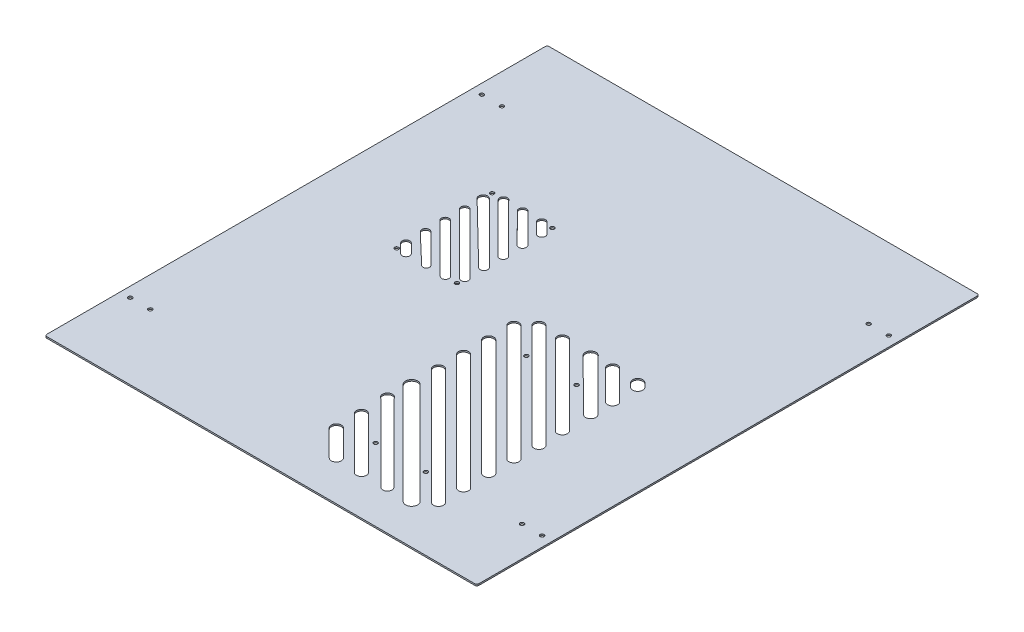
SolidWorks part; units mm, degrees
ref_plane "Front Plane" through (0, 0, 0) normal (0, 0, 1) x (1, 0, 0)
ref_plane "Top Plane" through (0, 0, 0) normal (0, 1, 0) x (1, 0, 0)
ref_plane "Right Plane" through (0, 0, 0) normal (1, 0, 0) x (0, 0, -1)
other "Center of Mass"
sketch "Sketch1" plane through (0, 0, 0) normal (0, 1, 0) x (1, 0, 0)
  line L1 (-215, -250) -> (215, -250)
  line L2 (-215, -250) -> (-215, 250)
  line L3 (-215, 250) -> (215, 250)
  line L4 (215, -250) -> (215, 250)
  line L5 (-215, -250) -> (215, 250) construction
  line L6 (-215, 250) -> (215, -250) construction
  point P0 (0, 0)
  dimension "D1" = 430
  dimension "D2" = 500
extrude "Boss-Extrude1" add sketch "Sketch1" along normal blind 1.5
sketch "Sketch6" plane through (0, 1.5, 0) normal (0, 1, 0) x (1, 0, 0)
  circle A0 centre (92.2927, -28) radius 1.95
  circle A1 centre (42.2927, -28) radius 1.95
  circle A2 centre (92.2927, -178) radius 1.95
  circle A3 centre (42.2927, -178) radius 1.95
  dimension "D1" = 50
  dimension "D2" = 150
sketch "Sketch7" plane through (0, 1.5, 0) normal (0, 1, 0) x (1, 0, 0)
  circle A0 centre (-114.98, 95.1924) radius 1.95
  circle A1 centre (-54.98, 95.1924) radius 1.95
  circle A2 centre (-54.98, 0.1924) radius 1.95
  circle A3 centre (-114.98, 0.1924) radius 1.95
  dimension "D1" = 95
  dimension "D2" = 60
sketch "Sketch12" plane through (0, 0, 0) normal (0, -1, 0) x (-1, 0, 0)
  line L2 (215, 250) -> (215, -250) construction
  line L3 (-215, -250) -> (-215, 250) construction
  circle A0 centre (-185, -175) radius 1.95
  circle A1 centre (-205, 170) radius 1.95
  circle A5 centre (-205, -175) radius 1.95
  circle A6 centre (-185, 170) radius 1.95
  circle A7 centre (205, -175) radius 1.95
  circle A9 centre (185, 175) radius 1.95
  circle A10 centre (205, 175) radius 1.95
  circle A11 centre (185, -175) radius 1.95
  dimension "D5" = 10
  dimension "D6" = 20
  dimension "D7" = 20
  dimension "D8" = 10
extrude "Cut-Extrude3" cut sketch "Sketch12" against normal blind 50.8
extrude "Cut-Extrude4" cut sketch "Sketch6" against normal blind 50.8
extrude "Cut-Extrude5" cut sketch "Sketch7" against normal blind 50.8
fillet "Fillet1" radius 2 4 edges at (215, 0.75, -250) (215, 0.75, 250) (-215, 0.75, 250) (-215, 0.75, -250)
sketch "Sketch13" plane through (0, 0, 0) normal (0, -1, 0) x (1, 0, 0)
  line L0 (67.2927, 28) -> (67.2927, 178) construction
  line L6 (92.2927, 178) -> (42.2927, 178) construction
  line L8 (92.2927, 178) -> (92.2927, 28) construction
  line L9 (92.2927, 28) -> (42.2927, 28) construction
  line L10 (42.2927, 178) -> (42.2927, 28) construction
  line L11 (67.2927, 103) -> (42.2927, 103) construction
  line L12 (124.7927, 122.9451) -> (9.7927, 7.9451) construction
  line L13 (124.7927, 210.5) -> (9.7927, 210.5)
  line L14 (124.7927, 210.5) -> (124.7927, -4.5)
  line L15 (124.7927, -4.5) -> (9.7927, -4.5)
  line L16 (9.7927, 210.5) -> (9.7927, -4.5)
  line L17 (124.7927, 210.5) -> (9.7927, -4.5) construction
  line L18 (124.7927, -4.5) -> (9.7927, 210.5) construction
  line L19 (128.3282, 119.4095) -> (13.3282, 4.4095)
  line L20 (121.2572, 126.4806) -> (6.2572, 11.4806)
  line L21 (124.7927, 147.9451) -> (9.7927, 32.9451) construction
  line L22 (128.3282, 144.4095) -> (13.3282, 29.4095)
  line L23 (121.2572, 151.4806) -> (6.2572, 36.4806)
  line L26 (124.7927, 172.9451) -> (9.7927, 57.9451) construction
  line L29 (128.3282, 169.4095) -> (13.3282, 54.4095)
  line L32 (121.2572, 176.4806) -> (6.2572, 61.4806)
  line L35 (124.7927, 197.9451) -> (9.7927, 82.9451) construction
  line L38 (128.3282, 194.4095) -> (13.3282, 79.4095)
  line L41 (121.2572, 201.4806) -> (6.2572, 86.4806)
  line L44 (110.6506, 210.5) -> (9.7927, 109.6421) construction
  line L47 (114.8916, 206.259) -> (14.0337, 105.4011)
  line L50 (102.1686, 210.5) -> (5.5517, 113.8831)
  line L53 (-54.98, -95.1924) -> (-114.98, -95.1924) construction
  line L58 (-114.98, -95.1924) -> (-114.98, -44.2867) construction
  line L62 (86.5307, 210.5) -> (8.6916, 132.661) construction
  line L65 (-114.98, -0.1924) -> (-54.98, -0.1924) construction
  line L66 (-54.98, -0.1924) -> (-54.98, -95.1924) construction
  line L67 (-54.98, -84.5868) -> (-65.5855, -95.1924) construction
  line L68 (-54.98, -89.8901) -> (-60.2822, -95.1924)
  line L69 (-57.6303, -81.9365) -> (-68.2358, -92.5421)
  line L70 (-54.98, -95.1924) -> (-114.98, -0.1924) construction
  line L71 (-54.98, -65.4331) -> (-84.7393, -95.1924) construction
  line L72 (-54.98, -70.7364) -> (-79.4324, -95.1924)
  line L73 (-57.6384, -62.7886) -> (-87.2428, -92.5491)
  line L74 (-54.98, -46.2793) -> (-103.893, -95.1924) construction
  line L75 (-54.98, -51.5826) -> (-98.5897, -95.1924)
  line L76 (-57.6398, -43.6363) -> (-106.2442, -92.5505)
  line L77 (-54.98, -27.1256) -> (-120.2706, -91.5396) construction
  line L78 (-54.98, -32.4289) -> (-111.9255, -89.3745)
  line L79 (-57.5955, -24.4383) -> (-117.9928, -83.2246)
  line L80 (-52.4189, -5.4139) -> (-114.98, -67.9718) construction
  line L81 (-52.3742, -10.6694) -> (-112.3283, -70.6235)
  line L83 (-63.9533, 2.3637) -> (-114.98, -48.8181) construction
  line L84 (-63.9494, -2.7446) -> (-112.3283, -51.1235)
  line L87 (-71.6576, -0.1924) -> (-114.98, -43.5148)
  line L88 (-85.508, -0.1924) -> (-114.98, -29.6644) construction
  line L91 (-83.2026, -2.4978) -> (-112.3283, -31.6235)
  line L92 (-90.2324, -0.1924) -> (-114.98, -23.7903)
  line L93 (-105.7005, -0.1924) -> (-114.98, -10.5106) construction
  line L96 (-103.0489, -2.844) -> (-112.3283, -12.1235)
  line L99 (-111.0038, -0.1924) -> (-114.98, -4.1685)
  line L102 (-60.2822, -95.1924) -> (-62.9366, -97.844)
  line L105 (-98.5897, -95.1924) -> (-100.7736, -97.6705)
  line L106 (-79.4324, -95.1924) -> (-81.8594, -97.7646)
  line L107 (-114.98, -62.6685) -> (-117.6316, -65.3202)
  line L108 (-114.98, -43.5148) -> (-117.4324, -45.635)
  line L109 (-114.98, -4.1685) -> (-117.6316, -6.8202)
  line L110 (-54.98, -89.8901) -> (-52.3283, -87.2358)
  line L111 (-54.98, -70.7364) -> (-52.3283, -68.0843)
  line L112 (-54.98, -51.5826) -> (-52.3283, -48.9306)
  line L113 (-54.98, -32.4289) -> (-52.3283, -29.7772)
  line L114 (-57.5857, -5.4578) -> (-114.98, -62.6685)
  line L115 (-90.2324, -0.1924) -> (-87.7579, 2.1672)
  line L116 (-71.6576, -0.1924) -> (-69.0283, 2.3851)
  line L117 (-111.0038, -0.1924) -> (-108.3522, 2.4593)
  line L118 (-114.98, -23.7903) -> (-117.5678, -26.2579)
  line L119 (89.7127, 207.318) -> (13.4147, 131.0201)
  line L120 (80.1667, 210.5) -> (7.0508, 137.3841)
  line L121 (60.6506, 210.5) -> (9.7927, 159.6421) construction
  line L122 (64.1861, 206.9645) -> (13.3282, 156.1066)
  line L123 (53.5795, 210.5) -> (6.2572, 163.1777)
  line L124 (35.6506, 210.5) -> (9.7927, 184.6421) construction
  line L125 (39.1861, 206.9645) -> (13.3282, 181.1066)
  line L126 (28.5795, 210.5) -> (6.2572, 188.1777)
  line L127 (10.6506, 210.5) -> (9.7927, 209.6421) construction
  line L128 (16.6674, 209.4458) -> (13.3282, 206.1066)
  line L130 (128.3284, -3.8936) -> (124.1859, -8.0357)
  line L133 (125.6429, 98.792) -> (22.3509, -4.5) construction
  line L134 (129.1784, 95.2564) -> (29.422, -4.5)
  line L135 (122.1073, 102.3275) -> (18.8154, -0.9645)
  line L136 (124.7927, 74.6421) -> (45.6506, -4.5) construction
  line L137 (128.3282, 71.1066) -> (52.7216, -4.5)
  line L138 (121.2572, 78.1777) -> (42.115, -0.9645)
  line L139 (124.7927, 46.436) -> (73.8567, -4.5) construction
  line L140 (128.4341, 42.7783) -> (80.9436, -4.5)
  line L141 (121.1513, 50.0937) -> (70.1015, -0.728)
  line L142 (124.7927, 24.6421) -> (95.6506, -4.5) construction
  line L143 (128.3282, 21.1066) -> (102.7216, -4.5)
  line L144 (121.2572, 28.1777) -> (92.115, -0.9645)
  line L145 (124.7928, -0.358) -> (120.6506, -4.5) construction
  line L147 (121.2572, 3.1777) -> (117.115, -0.9645)
  line L166 (6.6802, 213.5553) -> (10.376, 216.4949)
  line L167 (28.5795, 210.5) -> (32.115, 214.0355)
  line L168 (53.5795, 210.5) -> (57.115, 214.0355)
  line L169 (80.1667, 210.5) -> (83.3487, 213.682)
  line L170 (102.1686, 210.5) -> (106.4096, 214.741)
  line L171 (102.7216, -4.5) -> (99.1861, -8.0355)
  line L172 (80.9436, -4.5) -> (77.854, -8.0143)
  line L173 (52.7216, -4.5) -> (49.1861, -8.0355)
  line L174 (29.422, -4.5) -> (25.8864, -8.0355)
  line L392 (124.7927, 347.9451) -> (9.7927, 232.9451) construction
  line L393 (128.3282, 344.4095) -> (13.3282, 229.4095) [skipped]
  line L394 (121.2572, 351.4806) -> (6.2572, 236.4806) [skipped]
  line L395 (124.7927, 322.9451) -> (9.7927, 207.9451) construction
  line L396 (128.3282, 319.4095) -> (13.3282, 204.4095) [skipped]
  line L397 (121.2572, 326.4806) -> (6.2572, 211.4806) [skipped]
  line L398 (124.7927, 297.9451) -> (9.7927, 182.9451) construction
  line L399 (128.3282, 294.4095) -> (13.3282, 179.4095) [skipped]
  line L400 (121.2572, 301.4806) -> (6.2572, 186.4806) [skipped]
  line L401 (124.7927, 272.9451) -> (9.7927, 157.9451) construction
  line L402 (128.3282, 269.4095) -> (13.3282, 154.4095) [skipped]
  line L403 (121.2572, 276.4806) -> (6.2572, 161.4806) [skipped]
  line L404 (124.7927, 247.9451) -> (9.7927, 132.9451) construction
  line L405 (128.3282, 244.4095) -> (13.3282, 129.4095) [skipped]
  line L406 (121.2572, 251.4806) -> (6.2572, 136.4806) [skipped]
  line L407 (124.7927, 222.9451) -> (9.7927, 107.9451) construction
  line L408 (128.3282, 219.4095) -> (13.3282, 104.4095) [skipped]
  line L409 (121.2572, 226.4806) -> (6.2572, 111.4806) [skipped]
  line L410 (124.7927, 347.9451) -> (9.7927, 232.9451) construction
  line L411 (128.3282, 344.4095) -> (13.3282, 229.4095) [skipped]
  line L412 (121.2572, 351.4806) -> (6.2572, 236.4806) [skipped]
  line L413 (124.7927, 322.9451) -> (9.7927, 207.9451) construction
  line L414 (128.3282, 319.4095) -> (13.3282, 204.4095) [skipped]
  line L415 (121.2572, 326.4806) -> (6.2572, 211.4806) [skipped]
  line L416 (124.7927, 297.9451) -> (9.7927, 182.9451) construction
  line L417 (128.3282, 294.4095) -> (13.3282, 179.4095) [skipped]
  line L418 (121.2572, 301.4806) -> (6.2572, 186.4806) [skipped]
  line L419 (124.7927, 272.9451) -> (9.7927, 157.9451) construction
  line L420 (128.3282, 269.4095) -> (13.3282, 154.4095) [skipped]
  line L421 (121.2572, 276.4806) -> (6.2572, 161.4806) [skipped]
  line L422 (124.7927, 247.9451) -> (9.7927, 132.9451) construction
  line L423 (128.3282, 244.4095) -> (13.3282, 129.4095) [skipped]
  line L424 (121.2572, 251.4806) -> (6.2572, 136.4806) [skipped]
  line L425 (124.7927, 222.9451) -> (9.7927, 107.9451) construction
  line L426 (128.3282, 219.4095) -> (13.3282, 104.4095) [skipped]
  line L427 (121.2572, 226.4806) -> (6.2572, 111.4806) [skipped]
  arc A32 (128.3282, 119.4095) -> (121.2572, 126.4806) centre (124.7927, 122.9451) ccw
  arc A59 (-68.2358, -92.5421) -> (-62.9366, -97.844) centre (-65.5855, -95.1924) ccw
  arc A60 (-87.2428, -92.5491) -> (-81.8594, -97.7646) centre (-84.5855, -95.1924) ccw
  arc A61 (-106.2442, -92.5505) -> (-100.7736, -97.6705) centre (-103.5855, -95.1924) ccw
  arc A63 (-117.6316, -65.3202) -> (-112.3283, -70.6235) centre (-114.98, -67.9718) ccw
  arc A64 (-117.4324, -45.635) -> (-112.3283, -51.1235) centre (-114.98, -48.4718) ccw
  arc A65 (-117.5678, -26.2579) -> (-112.3283, -31.6235) centre (-114.98, -28.9718) ccw
  arc A66 (-117.6316, -6.8202) -> (-112.3283, -12.1235) centre (-114.98, -9.4718) ccw
  arc A67 (-52.3283, -29.7772) -> (-57.5955, -24.4383) centre (-54.98, -27.1256) ccw
  arc A68 (-52.3283, -48.9306) -> (-57.6398, -43.6363) centre (-54.98, -46.2793) ccw
  arc A69 (-52.3283, -68.0843) -> (-57.6384, -62.7886) centre (-54.98, -65.4331) ccw
  arc A70 (-52.3283, -87.2358) -> (-57.6303, -81.9365) centre (-54.98, -84.5868) ccw
  arc A71 (-52.3742, -10.6694) -> (-57.5857, -5.4578) centre (-54.98, -8.0636) ccw
  arc A72 (-117.9928, -83.2246) -> (-111.9255, -89.3745) centre (-114.98, -86.32) ccw
  arc A73 (6.2572, 11.4806) -> (13.3282, 4.4095) centre (9.7927, 7.9451) ccw
  arc A74 (128.3282, 144.4095) -> (121.2572, 151.4806) centre (124.7927, 147.9451) ccw
  arc A75 (6.2572, 36.4806) -> (13.3282, 29.4095) centre (9.7927, 32.9451) ccw
  arc A76 (128.3282, 169.4095) -> (121.2572, 176.4806) centre (124.7927, 172.9451) ccw
  arc A77 (6.2572, 61.4806) -> (13.3282, 54.4095) centre (9.7927, 57.9451) ccw
  circle A78 centre (-122.5855, -95.1924) radius 3.7481 [skipped]
  arc A79 (-83.2026, -2.4978) -> (-87.7579, 2.1672) centre (-85.508, -0.1924) ccw
  arc A80 (-103.0489, -2.844) -> (-108.3522, 2.4593) centre (-105.7005, -0.1924) ccw
  arc A81 (-63.9494, -2.7446) -> (-69.0283, 2.3851) centre (-66.5016, -0.1924) ccw
  arc A82 (128.3282, 194.4095) -> (121.2572, 201.4806) centre (124.7927, 197.9451) ccw
  arc A83 (6.2572, 86.4806) -> (13.3282, 79.4095) centre (9.7927, 82.9451) ccw
  arc A85 (5.5517, 113.8831) -> (14.0337, 105.4011) centre (9.7927, 109.6421) ccw
  arc A87 (7.0508, 137.3841) -> (13.4147, 131.0201) centre (8.6916, 132.661) ccw
  arc A89 (6.2572, 163.1777) -> (13.3282, 156.1066) centre (9.7927, 159.6421) ccw
  arc A91 (6.2572, 188.1777) -> (13.3282, 181.1066) centre (9.7927, 184.6421) ccw
  arc A93 (6.6802, 213.5553) -> (13.3282, 206.1066) centre (9.7927, 209.6421) ccw
  arc A96 (129.1784, 95.2564) -> (122.1073, 102.3275) centre (125.6429, 98.792) ccw
  arc A98 (128.3282, 71.1066) -> (121.2572, 78.1777) centre (124.7927, 74.6421) ccw
  arc A100 (128.4341, 42.7783) -> (121.1513, 50.0937) centre (124.7927, 46.436) ccw
  arc A102 (128.3282, 21.1066) -> (121.2572, 28.1777) centre (124.7927, 24.6421) ccw
  arc A104 (128.3284, -3.8936) -> (121.2572, 3.1777) centre (124.7928, -0.358) ccw
  arc A118 (117.115, -0.9645) -> (124.1859, -8.0357) centre (120.6506, -4.5) ccw
  arc A119 (92.115, -0.9645) -> (99.1861, -8.0355) centre (95.6506, -4.5) ccw
  arc A120 (70.1015, -0.728) -> (77.854, -8.0143) centre (73.8567, -4.5) ccw
  arc A121 (42.115, -0.9645) -> (49.1861, -8.0355) centre (45.6506, -4.5) ccw
  arc A122 (18.8154, -0.9645) -> (25.8864, -8.0355) centre (22.3509, -4.5) ccw
  arc A123 (114.8916, 206.259) -> (106.4096, 214.741) centre (110.6506, 210.5) ccw
  arc A124 (89.7127, 207.318) -> (83.3487, 213.682) centre (86.5307, 210.5) ccw
  arc A125 (64.1861, 206.9645) -> (57.115, 214.0355) centre (60.6506, 210.5) ccw
  arc A126 (39.1861, 206.9645) -> (32.115, 214.0355) centre (35.6506, 210.5) ccw
  arc A127 (16.6674, 209.4458) -> (10.376, 216.4949) centre (13.3216, 212.7917) ccw
  arc A285 (128.3282, 344.4095) -> (121.2572, 351.4806) centre (124.7927, 347.9451) ccw [skipped]
  arc A286 (6.2572, 236.4806) -> (13.3282, 229.4095) centre (9.7927, 232.9451) ccw [skipped]
  arc A287 (128.3282, 319.4095) -> (121.2572, 326.4806) centre (124.7927, 322.9451) ccw [skipped]
  arc A288 (6.2572, 211.4806) -> (13.3282, 204.4095) centre (9.7927, 207.9451) ccw [skipped]
  arc A289 (128.3282, 294.4095) -> (121.2572, 301.4806) centre (124.7927, 297.9451) ccw [skipped]
  arc A290 (6.2572, 186.4806) -> (13.3282, 179.4095) centre (9.7927, 182.9451) ccw [skipped]
  arc A291 (128.3282, 269.4095) -> (121.2572, 276.4806) centre (124.7927, 272.9451) ccw [skipped]
  arc A292 (6.2572, 161.4806) -> (13.3282, 154.4095) centre (9.7927, 157.9451) ccw [skipped]
  arc A293 (128.3282, 244.4095) -> (121.2572, 251.4806) centre (124.7927, 247.9451) ccw [skipped]
  arc A294 (6.2572, 136.4806) -> (13.3282, 129.4095) centre (9.7927, 132.9451) ccw [skipped]
  arc A295 (128.3282, 219.4095) -> (121.2572, 226.4806) centre (124.7927, 222.9451) ccw [skipped]
  arc A296 (6.2572, 111.4806) -> (13.3282, 104.4095) centre (9.7927, 107.9451) ccw [skipped]
  point P18 (67.2927, 65.4451)
  point P23 (67.2927, 90.4451)
  point P30 (67.2927, 115.4451)
  point P37 (67.2927, 140.4451)
  point P46 (67.2927, 167.1421)
  point P54 (67.2927, 192.1421)
  point P73 (67.2927, 217.1421)
  point P85 (67.2927, 153)
  point P89 (-59.0853, -88.6922)
  point P94 (67.2927, 42.1421)
  point P102 (67.2927, 17.1421)
  point P116 (67.2927, 193)
  point P124 (-66.4512, -76.9043)
  point P125 (67.2927, 173)
  point P135 (-73.8171, -65.1165)
  point P151 (-81.183, -53.3286)
  point P153 (67.2927, 193)
  point P156 (67.2927, 292.1421)
  point P159 (-88.5489, -41.5407)
  point P160 (67.2927, 173)
  point P167 (67.2927, 153)
  point P168 (-95.9147, -29.7529)
  point P174 (67.2927, 193)
  point P176 (-103.2806, -17.965)
  point P181 (67.2927, 173)
  point P184 (-110.6465, -6.1771)
  point P188 (67.2927, 153)
  point P207 (67.2927, 267.1421)
  point P227 (67.2927, 242.1421)
  point P235 (67.2927, 192.1421)
  point P242 (67.2927, 167.1421)
  point P251 (67.2927, 193)
  point P258 (67.2927, 173)
  point P265 (67.2927, 153)
  point P272 (67.2927, 193)
  point P279 (67.2927, 173)
  point P286 (67.2927, 153)
  point P321 (67.2927, 193)
  point P328 (67.2927, 173)
  point P335 (67.2927, 153)
  point P342 (67.2927, 193)
  point P349 (67.2927, 173)
  point P356 (67.2927, 153)
  point P365 (67.2927, 193)
  point P372 (67.2927, 173)
  point P379 (67.2927, 153)
  point P386 (67.2927, 193)
  point P393 (67.2927, 173)
  point P400 (67.2927, 153)
  point P407 (67.2927, 193)
  point P414 (67.2927, 173)
  point P421 (67.2927, 153)
  point P428 (67.2927, 193)
  point P435 (67.2927, 173)
  point P442 (67.2927, 153)
  point P449 (67.2927, 193)
  point P456 (67.2927, 173)
  point P463 (67.2927, 153)
  point P470 (67.2927, 193)
  point P477 (67.2927, 173)
  point P484 (67.2927, 153)
  point P491 (67.2927, 193)
  point P498 (67.2927, 173)
  point P505 (67.2927, 153)
  point P512 (67.2927, 193)
  point P519 (67.2927, 173)
  point P526 (67.2927, 153)
  point P533 (67.2927, 193)
  point P540 (67.2927, 173)
  point P547 (67.2927, 153)
  point P554 (67.2927, 193)
  point P561 (67.2927, 173)
  point P568 (67.2927, 153)
  point P575 (67.2927, 193)
  point P582 (67.2927, 173)
  point P589 (67.2927, 153)
  point P596 (67.2927, 193)
  point P603 (67.2927, 173)
  point P610 (67.2927, 153)
  point P617 (67.2927, 193)
  point P624 (67.2927, 173)
  point P631 (67.2927, 153)
  point P638 (67.2927, 193)
  point P645 (67.2927, 173)
  point P652 (67.2927, 153)
  point P677 (67.2927, 292.1421)
  point P684 (67.2927, 267.1421)
  point P691 (67.2927, 242.1421)
  point P698 (67.2927, 217.1421)
  point P705 (67.2927, 192.1421)
  point P712 (67.2927, 167.1421)
  point P719 (67.2927, 288.6066)
  point P726 (67.2927, 263.6066)
  point P733 (67.2927, 238.6066)
  point P740 (67.2927, 213.6066)
  point P747 (67.2927, 188.6066)
  point P754 (67.2927, 163.6066)
  point P761 (67.2927, 288.6066)
  point P768 (67.2927, 263.6066)
  point P775 (67.2927, 238.6066)
  point P782 (67.2927, 213.6066)
  point P789 (67.2927, 188.6066)
  point P796 (67.2927, 163.6066)
  point P803 (67.2927, 288.6066)
  point P810 (67.2927, 263.6066)
  point P817 (67.2927, 238.6066)
  point P824 (67.2927, 213.6066)
  point P831 (67.2927, 188.6066)
  point P838 (67.2927, 163.6066)
  point P845 (67.2927, 288.6066)
  point P852 (67.2927, 263.6066)
  point P859 (67.2927, 238.6066)
  point P866 (67.2927, 213.6066)
  point P873 (67.2927, 188.6066)
  point P880 (67.2927, 163.6066)
  point P887 (67.2927, 288.6066)
  point P894 (67.2927, 263.6066)
  point P901 (67.2927, 238.6066)
  point P908 (67.2927, 213.6066)
  point P915 (67.2927, 188.6066)
  point P922 (67.2927, 163.6066)
  point P929 (67.2927, 288.6066)
  point P936 (67.2927, 263.6066)
  point P943 (67.2927, 238.6066)
  point P950 (67.2927, 213.6066)
  point P957 (67.2927, 188.6066)
  point P964 (67.2927, 163.6066)
  point P971 (67.2927, 289.3137)
  point P978 (67.2927, 264.3137)
  point P985 (67.2927, 239.3137)
  point P992 (67.2927, 214.3137)
  point P999 (67.2927, 189.3137)
  point P1006 (67.2927, 164.3137)
  point P1013 (67.2927, 289.3137)
  point P1020 (67.2927, 264.3137)
  point P1027 (67.2927, 239.3137)
  point P1034 (67.2927, 214.3137)
  point P1041 (67.2927, 189.3137)
  point P1048 (67.2927, 164.3137)
  point P1055 (67.2927, 290.4451)
  point P1062 (67.2927, 265.4451)
  point P1069 (67.2927, 240.4451)
  point P1076 (67.2927, 215.4451)
  point P1083 (67.2927, 190.4451)
  point P1090 (67.2927, 165.4451)
  point P1097 (67.2927, 290.4451)
  point P1104 (67.2927, 265.4451)
  point P1111 (67.2927, 240.4451)
  point P1118 (67.2927, 215.4451)
  point P1125 (67.2927, 190.4451)
  point P1132 (67.2927, 165.4451)
  point P1139 (67.2927, 290.4451)
  point P1146 (67.2927, 265.4451)
  point P1153 (67.2927, 240.4451)
  point P1160 (67.2927, 215.4451)
  point P1167 (67.2927, 190.4451)
  point P1174 (67.2927, 165.4451)
  point P1181 (67.2927, 290.4451)
  point P1188 (67.2927, 265.4451)
  point P1195 (67.2927, 240.4451)
  point P1202 (67.2927, 215.4451)
  point P1209 (67.2927, 190.4451)
  point P1216 (67.2927, 165.4451)
  point P1223 (67.2927, 290.4451)
  point P1230 (67.2927, 265.4451)
  point P1237 (67.2927, 240.4451)
  point P1244 (67.2927, 215.4451)
  point P1251 (67.2927, 190.4451)
  point P1258 (67.2927, 165.4451)
  dimension "D1" = 115
  dimension "D5" = 45
  dimension "D6" = 4
  dimension "D7" = 4
  dimension "D8" = 45
  dimension "D9" = 3.8
  dimension "D10" = 10
  dimension "D2" = 215
  dimension "D3" = 45
  dimension "D4" = 5
  dimension "D11" = 7.68
  dimension "D12" = 10
  dimension "D13" = 9
  dimension "D14" = 45
  dimension "D15" = 45
  dimension "D16" = 5
  dimension "D17" = 3.8
extrude "Cut-Extrude6" cut sketch "Sketch13" against normal blind 10
